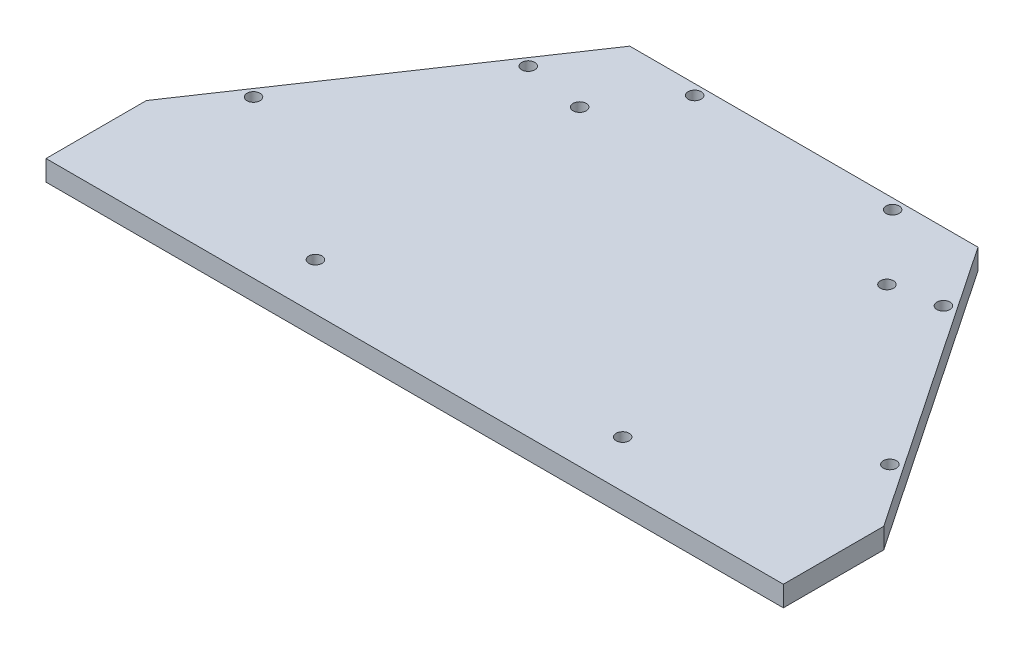
SolidWorks part; units mm, degrees
ref_plane "Front Plane" through (0, 0, 0) normal (0, 0, 1) x (1, 0, 0)
ref_plane "Top Plane" through (0, 0, 0) normal (0, 1, 0) x (1, 0, 0)
ref_plane "Right Plane" through (0, 0, 0) normal (1, 0, 0) x (0, 0, -1)
sketch "Sketch1" plane through (0, 0, 0) normal (0, 1, 0) x (1, 0, 0)
  line L0 (44.7332, 23.709) -> (-40.2668, 23.709)
  line L1 (-40.2668, 23.709) -> (-87.7613, -46.7841)
  line L2 (44.7332, 23.709) -> (92.2277, -46.7841)
  line L4 (-87.7613, -46.7841) -> (-87.7613, -71.2941)
  line L5 (-87.7613, -71.2941) -> (92.2277, -71.2941)
  line L6 (92.2277, -46.7841) -> (92.2277, -71.2941)
  point P3 (2.2332, 23.709)
  dimension "D1" = 236.03
  dimension "D2" = 85
  dimension "D3" = 85
  dimension "D4" = 85
  dimension "D5" = 236.03
  dimension "D6" = 24.51
  dimension "D7" = 146.03
  dimension "D8" = 24.51
extrude "Boss-Extrude1" add sketch "Sketch1" along normal blind 5
sketch "Sketch2" plane through (0, 5, 0) normal (0, 1, 0) x (1, 0, 0)
  line L0 (44.7332, 23.709) -> (-40.2668, 23.709) construction
  line L1 (2.2332, 23.709) -> (2.2332, 0) construction
  line L2 (-40.2668, 23.709) -> (-87.7613, -46.7841) construction
  line L3 (-64.014, -11.5376) -> (-20.5069, -40.8504) construction
  circle A0 centre (-21.9275, 21.209) radius 1.6
  circle A1 centre (26.3939, 21.209) radius 1.6
  circle A2 centre (-48.4433, 7.099) radius 1.6
  circle A3 centre (-75.4382, -32.9679) radius 1.6
  circle A4 centre (52.9097, 7.099) radius 1.6
  circle A5 centre (79.9046, -32.9679) radius 1.6
  dimension "D2" = 3.2
  dimension "D5" = 3.2
  dimension "D1" = 2.5
  dimension "D3" = 16.6062
  dimension "D4" = 2.5
  dimension "D6" = 16.61
extrude "Cut-Extrude1" cut sketch "Sketch2" against normal blind 10
sketch "Sketch3" plane through (0, 5, 0) normal (0, 1, 0) x (1, 0, 0)
  line L0 (44.7332, 23.709) -> (-40.2668, 23.709) construction
  line L1 (-37.4926, 8.709) -> (45.5074, 8.709) construction
  line L2 (-37.4926, 8.709) -> (-37.4926, -63.791) construction
  line L3 (-37.4926, -63.791) -> (45.5074, -63.791) construction
  line L4 (45.5074, 8.709) -> (45.5074, -63.791) construction
  line L5 (-37.4926, 8.709) -> (45.5074, -63.791) construction
  line L6 (-37.4926, -63.791) -> (45.5074, 8.709) construction
  line L7 (-40.2668, 23.709) -> (-87.7613, -46.7841) construction
  line L8 (4.0074, 8.709) -> (4.0074, -17.6324) construction
  line L9 (-37.4926, -27.541) -> (-8.9065, -27.541) construction
  circle A0 centre (-33.4926, 4.709) radius 1.6
  circle A1 centre (41.5074, 4.709) radius 1.6
  circle A2 centre (41.5074, -59.791) radius 1.6
  circle A3 centre (-33.4926, -59.791) radius 1.6
  point P4 (4.0074, -27.541)
  dimension "D5" = 3.2
  dimension "D1" = 83
  dimension "D2" = 72.5
  dimension "D3" = 15
  dimension "D4" = 33.97
  dimension "D6" = 4
  dimension "D7" = 4
extrude "Cut-Extrude2" cut sketch "Sketch3" against normal blind 13
sketch "Sketch4" plane through (0, 0, 0) normal (0, -1, 0) x (1, 0, 0)
  line L0 (2.2332, -23.709) -> (2.2332, 9.0902) construction
  line L1 (44.7332, -23.709) -> (-40.2668, -23.709) construction
  circle A0 centre (41.5074, -4.709) radius 2.8
  dimension "D1" = 5.6
sketch "Sketch5" plane through (0, 0, 0) normal (0, -1, 0) x (-1, 0, 0)
  circle A0 centre (33.4926, 4.709) radius 2.8
  circle A1 centre (33.4926, -59.791) radius 2.8
  circle A2 centre (-41.5074, -59.791) radius 2.8
  dimension "D1" = 5.6
  dimension "D2" = 5.6
  dimension "D3" = 5.6
extrude "Cut-Extrude3" cut sketch "Sketch5" against normal blind 1
extrude "Cut-Extrude4" cut sketch "Sketch4" against normal blind 1
